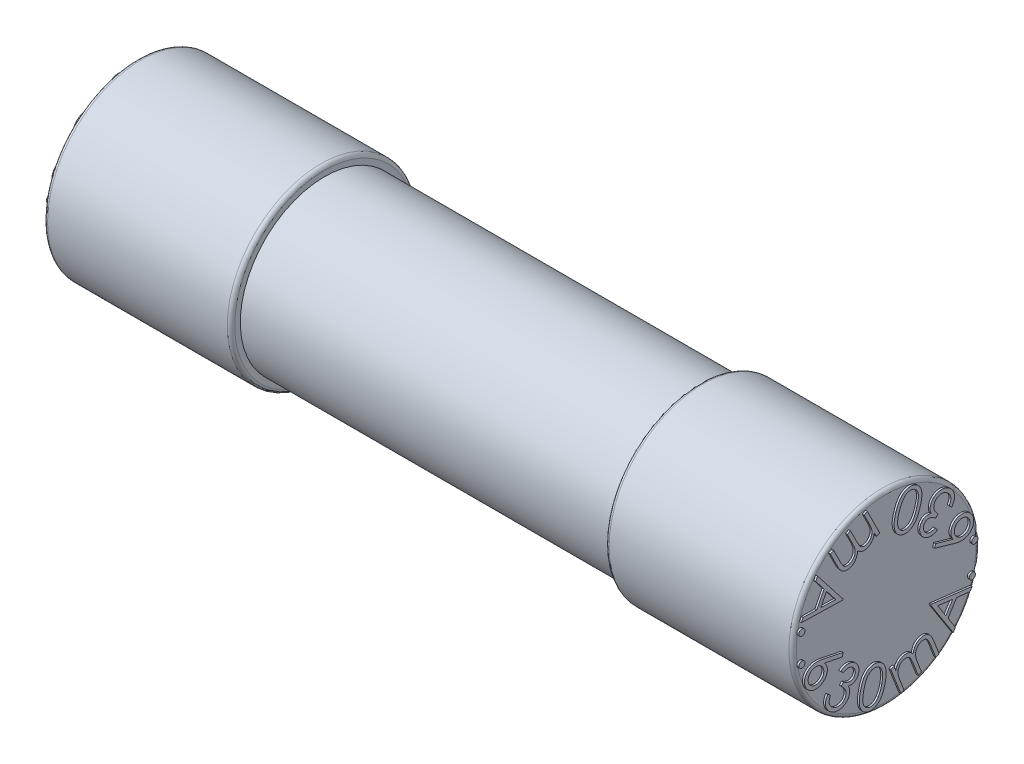
SolidWorks part; units mm, degrees
material "AISI 304"
ref_plane "Piano frontale" through (0, 0, 0) normal (0, 0, 1) x (1, 0, 0)
ref_plane "Piano superiore" through (0, 0, 0) normal (0, 1, 0) x (1, 0, 0)
ref_plane "Piano destro" through (0, 0, 0) normal (1, 0, 0) x (0, 0, -1)
sketch "Schizzo4" plane through (0, 0, 0) normal (0, 0, 1) x (1, 0, 0)
  line L0 (0, 0) -> (-9.75, 0) construction
  line L1 (-9.75, 0) -> (-9.75, 2.25)
  line L2 (-9.75, 2.25) -> (9.75, 2.25)
  line L3 (9.75, 2.25) -> (9.75, 0)
  line L4 (9.75, 0) -> (0, 0) construction
  line L5 (-9.75, 2) -> (9.75, 2)
  dimension "D1" = 19.5
  dimension "D2" = 2.25
  dimension "D3" = 0.25
revolve "Rivoluzione3" add sketch "Schizzo4" angle 360 about L0
sketch "Schizzo6" plane through (0, 0, 0) normal (0, 0, 1) x (1, 0, 0)
  line L0 (9.75, 0) -> (-9.75, 0)
  line L1 (-9.75, 2.25) -> (-9.75, -2.25) construction
  line L2 (-9.75, 0) -> (-10, 0)
  line L3 (-10, 0) -> (-10, 2.5)
  line L4 (-10, 2.5) -> (-5, 2.5)
  line L5 (-5, 2.5) -> (-5, 2.25)
  line L6 (9.75, 2.25) -> (-9.75, 2.25) construction
  line L7 (-5, 2.25) -> (-9.75, 2.25)
  line L8 (-9.75, 2.25) -> (-9.75, 0.1)
  line L9 (-9.75, 0.1) -> (9.75, 0.1)
  line L10 (0, 0.1) -> (0, 0)
  line L11 (0, 0) -> (0, -2.25) construction
  line L12 (-9.75, -2.25) -> (9.75, -2.25) construction
  line L13 (9.75, 2.25) -> (9.75, 0.1)
  line L14 (5, 2.25) -> (9.75, 2.25)
  line L15 (5, 2.5) -> (5, 2.25)
  line L16 (10, 2.5) -> (5, 2.5)
  line L17 (10, 0) -> (10, 2.5)
  line L18 (9.75, 0) -> (10, 0)
  dimension "D1" = 0.25
  dimension "D2" = 5
  dimension "D3" = 2.5
  dimension "D4" = 0.1
revolve "Rivoluzione4" add sketch "Schizzo6" angle 360 about L0
fillet "Raccordo1" radius 0.1 4 edges at (-10, 0, -2.5) (-5, 0, -2.5) (10, 0, -2.5) (5, 0, -2.5)
sketch "Schizzo7" plane through (-10, 0, 0) normal (-1, 0, 0) x (0, 0, 1)
  text T0 ".6 3 0  m A. .6 3 0 m A." font "Century Gothic" height 1
extrude "Estrusione-Estrusione4" add sketch "Schizzo7" along normal blind 0.05
sketch "Schizzo8" plane through (10, 0, 0) normal (1, 0, 0) x (0, 0, -1)
  text T0 ".6 3 0  m A. .6 3 0 m A." font "Century Gothic" height 1
extrude "Estrusione-Estrusione5" add sketch "Schizzo8" along normal blind 0.05
